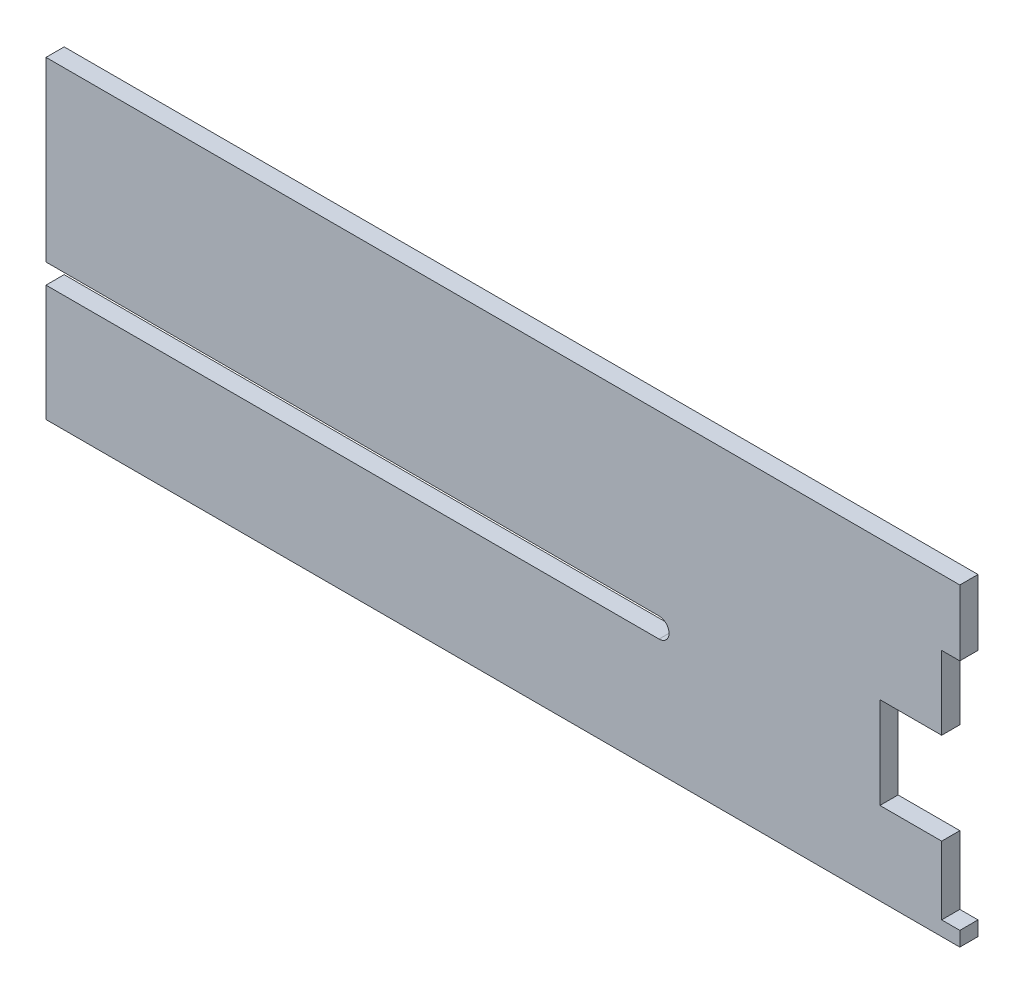
SolidWorks part; units mm, degrees
ref_plane "Front" through (0, 0, 0) normal (0, 0, 1) x (1, 0, 0)
ref_plane "Top" through (0, 0, 0) normal (0, 1, 0) x (1, 0, 0)
ref_plane "Right" through (0, 0, 0) normal (1, 0, 0) x (0, 0, -1)
sketch "Sketch1" plane through (0, 0, 0) normal (0, 0, 1) x (1, 0, 0)
  line L0 (-5, 13.8826) -> (-5, 8.9026)
  line L1 (-251.5843, 0) -> (0, 0)
  line L2 (-251.5843, 86.3509) -> (-251.5843, 37.5484)
  line L3 (-251.5843, 86.3509) -> (0, 86.3509)
  line L4 (0, 0) -> (0, 4)
  line L7 (-251.5843, 32.0484) -> (-82.8102, 32.0484)
  line L8 (-251.5843, 32.0484) -> (-251.5843, 0)
  line L9 (-251.5843, 37.5484) -> (-82.8102, 37.5484)
  line L10 (-5, 48.0065) -> (-22, 48.0065)
  line L12 (-5, 22.7794) -> (-22, 22.7794)
  line L13 (-22, 48.0065) -> (-22, 22.7794)
  line L14 (0, 68.2477) -> (0, 86.3509)
  line L18 (-22, 18.3222) -> (-22, 52.4636) construction
  line L19 (-5, 68.5164) -> (-5, 64.178) construction
  line L20 (0, 68.2477) -> (-5, 68.2477)
  line L21 (-5, 22.7794) -> (-5, 13.8826)
  line L22 (0, 4) -> (-5, 4)
  line L23 (-5, 68.2477) -> (-5, 48.0065)
  line L25 (-5, 13.8826) -> (-23, 13.8826) construction
  line L26 (-5, 8.9026) -> (-5, 4)
  line L27 (-5, 8.9026) -> (-23, 8.9026) construction
  line L28 (-23, 13.8826) -> (-23, 8.9026) construction
  arc A1 (-82.8102, 32.0484) -> (-82.8102, 37.5484) centre (-82.8102, 34.7984) ccw
  point P0 (0, 0)
  dimension "D1" = 5.5
extrude "Boss-Extrude1" add sketch "Sketch1" against normal blind 5
